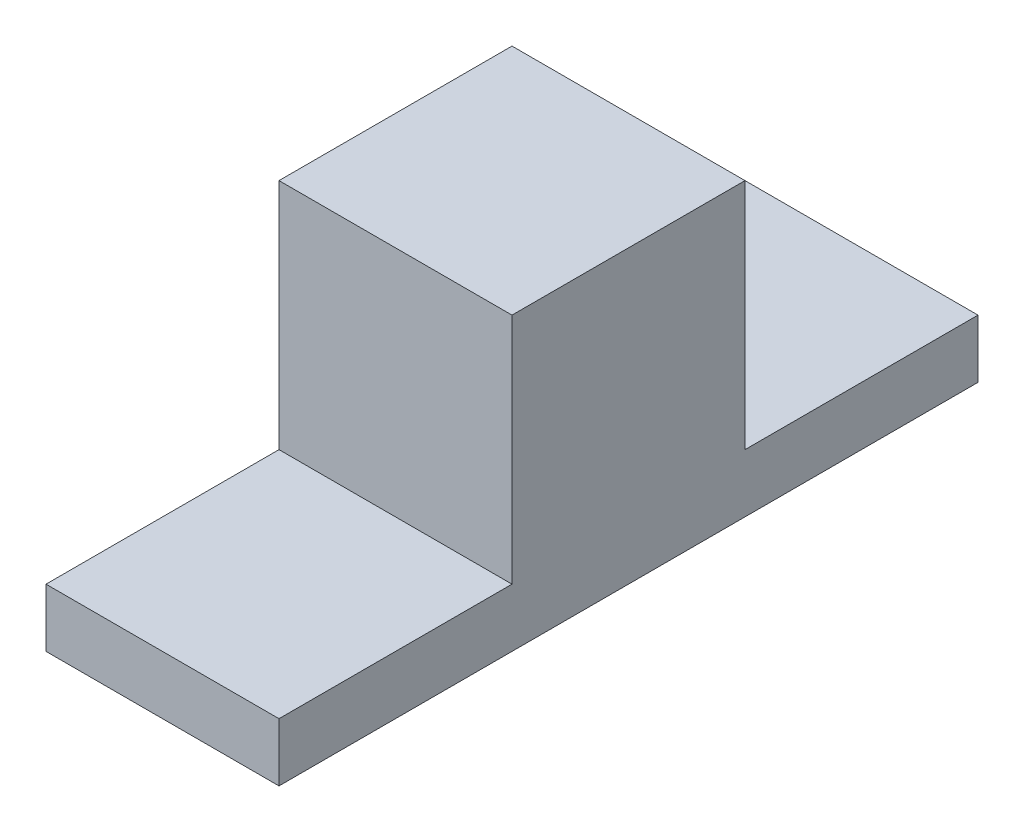
SolidWorks part; units mm, degrees
material "Acrylic (Medium-high impact)"
ref_plane "Front" through (0, 0, 0) normal (0, 0, 1) x (1, 0, 0)
ref_plane "Top" through (0, 0, 0) normal (0, 1, 0) x (1, 0, 0)
ref_plane "Right" through (0, 0, 0) normal (1, 0, 0) x (0, 0, -1)
sketch "Sketch2" plane through (0, 0, 0) normal (1, 0, 0) x (0, 0, -1)
  line L0 (3.175, 0) -> (9.525, 0)
  line L1 (-9.525, 0) -> (-3.175, 0)
  line L2 (-9.525, 0) -> (-9.525, -1.5875)
  line L3 (-9.525, -1.5875) -> (9.525, -1.5875)
  line L4 (9.525, 0) -> (9.525, -1.5875)
  line L6 (3.175, 0) -> (3.175, 6.35)
  line L7 (3.175, 6.35) -> (-3.175, 6.35)
  line L8 (-3.175, 0) -> (-3.175, 6.35)
  point P11 (0, 6.35)
  point P14 (0, -1.5875)
  dimension "D1" = 6.35
  dimension "D2" = 19.05
  dimension "D3" = 6.35
  dimension "D4" = 1.5875
extrude "Boss-Extrude1" add sketch "Sketch2" along normal blind 6.35
